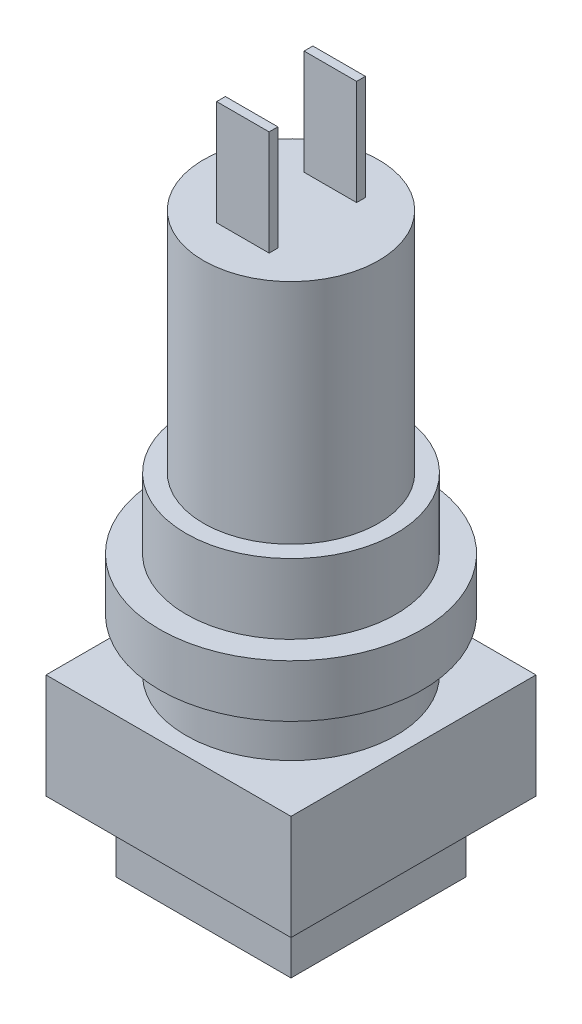
SolidWorks part; units mm, degrees
ref_plane "Front Plane" through (0, 0, 0) normal (0, 0, 1) x (1, 0, 0)
ref_plane "Top Plane" through (0, 0, 0) normal (0, 1, 0) x (1, 0, 0)
ref_plane "Right Plane" through (0, 0, 0) normal (1, 0, 0) x (0, 0, -1)
sketch "Sketch1" plane through (0, 0, 0) normal (0, 1, 0) x (1, 0, 0)
  line L1 (5, -5) -> (-5, -5)
  line L2 (5, -5) -> (5, 5)
  line L3 (5, 5) -> (-5, 5)
  line L4 (-5, -5) -> (-5, 5)
  line L5 (5, -5) -> (-5, 5) construction
  line L6 (5, 5) -> (-5, -5) construction
  point P0 (0, 0)
  dimension "D1" = 10
  dimension "D2" = 10
extrude "Boss-Extrude1" add sketch "Sketch1" along normal blind 4
sketch "Sketch2" plane through (0, 4, 0) normal (0, 1, 0) x (1, 0, 0)
  line L1 (-7, 7) -> (7, 7)
  line L2 (-7, 7) -> (-7, -7)
  line L3 (-7, -7) -> (7, -7)
  line L4 (7, 7) -> (7, -7)
  line L5 (-7, 7) -> (7, -7) construction
  line L6 (-7, -7) -> (7, 7) construction
  point P0 (0, 0)
  dimension "D1" = 14
  dimension "D2" = 14
extrude "Boss-Extrude2" add sketch "Sketch2" along normal blind 6
sketch "Sketch3" plane through (0, 10, 0) normal (0, 1, 0) x (1, 0, 0)
  circle A0 centre (0, 0) radius 6
  dimension "D1" = 12
extrude "Boss-Extrude3" add sketch "Sketch3" along normal blind 3
sketch "Sketch4" plane through (0, 13, 0) normal (0, 1, 0) x (1, 0, 0)
  circle A0 centre (0, 0) radius 7.5
  dimension "D1" = 15
extrude "Boss-Extrude4" add sketch "Sketch4" along normal blind 3
sketch "Sketch5" plane through (0, 16, 0) normal (0, 1, 0) x (1, 0, 0)
  circle A0 centre (0, 0) radius 6
  dimension "D1" = 12
extrude "Boss-Extrude5" add sketch "Sketch5" along normal blind 4
sketch "Sketch6" plane through (0, 20, 0) normal (0, 1, 0) x (1, 0, 0)
  circle A0 centre (0, 0) radius 5
  dimension "D1" = 10
extrude "Boss-Extrude6" add sketch "Sketch6" along normal blind 13
sketch "Sketch7" plane through (0, 33, 0) normal (0, 1, 0) x (1, 0, 0)
  line L0 (0, 0) -> (5, 0)
  line L1 (5, 0) -> (-5, 0)
  line L2 (0, 0) -> (0, 2.5)
  line L3 (-1.5, -2.25) -> (-1.5, -2.75)
  line L4 (-1.5, 2.25) -> (1.5, 2.25)
  line L5 (-1.5, 2.25) -> (-1.5, 2.75)
  line L6 (-1.5, 2.75) -> (1.5, 2.75)
  line L7 (1.5, 2.25) -> (1.5, 2.75)
  line L8 (-1.5, 2.25) -> (1.5, 2.75) construction
  line L9 (-1.5, 2.75) -> (1.5, 2.25) construction
  line L10 (1.5, -2.25) -> (1.5, -2.75)
  line L11 (-1.5, -2.75) -> (1.5, -2.75)
  line L12 (-1.5, -2.25) -> (1.5, -2.25)
  circle A1 centre (0, 0) radius 5
  circle A2 centre (0, 0) radius 5
  dimension "D2" = 2.5
  dimension "D3" = 3
  dimension "D4" = 0.5
  dimension "D1" = 0
extrude "Boss-Extrude7" add sketch "Sketch7" along normal blind 6
